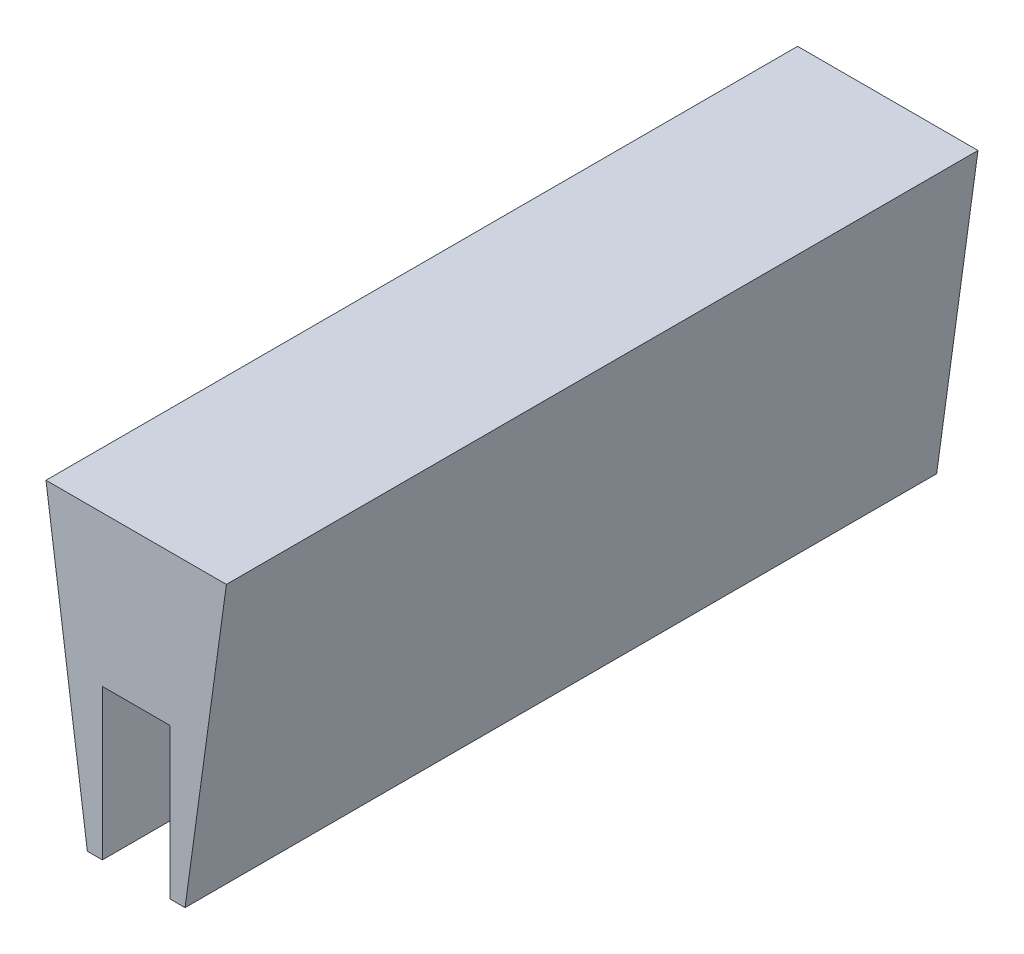
SolidWorks part; units mm, degrees
ref_plane "Front" through (0, 0, 0) normal (0, 0, 1) x (1, 0, 0)
ref_plane "Top" through (0, 0, 0) normal (0, 1, 0) x (1, 0, 0)
ref_plane "Right" through (0, 0, 0) normal (1, 0, 0) x (0, 0, -1)
sketch "Sketch1" plane through (0, 0, 0) normal (0, 0, 1) x (1, 0, 0)
  line L0 (0, 0) -> (0, 14758.4074) construction
  line L1 (-6, 20) -> (6, 20)
  line L2 (6, 20) -> (3.25, 0)
  line L3 (3.25, 0) -> (2.25, 0)
  line L4 (2.25, 0) -> (2.25, 10)
  line L5 (2.25, 10) -> (-2.25, 10)
  line L6 (-2.25, 0) -> (-2.25, 10)
  line L7 (-3.25, 0) -> (-2.25, 0)
  line L8 (-6, 20) -> (-3.25, 0)
  point P10 (0, 10)
  point P13 (0, 20)
  dimension "D1" = 4.5
  dimension "D2" = 10
  dimension "D3" = 10
  dimension "D4" = 6
  dimension "D5" = 1
extrude "Boss-Extrude1" add sketch "Sketch1" along normal blind 50
